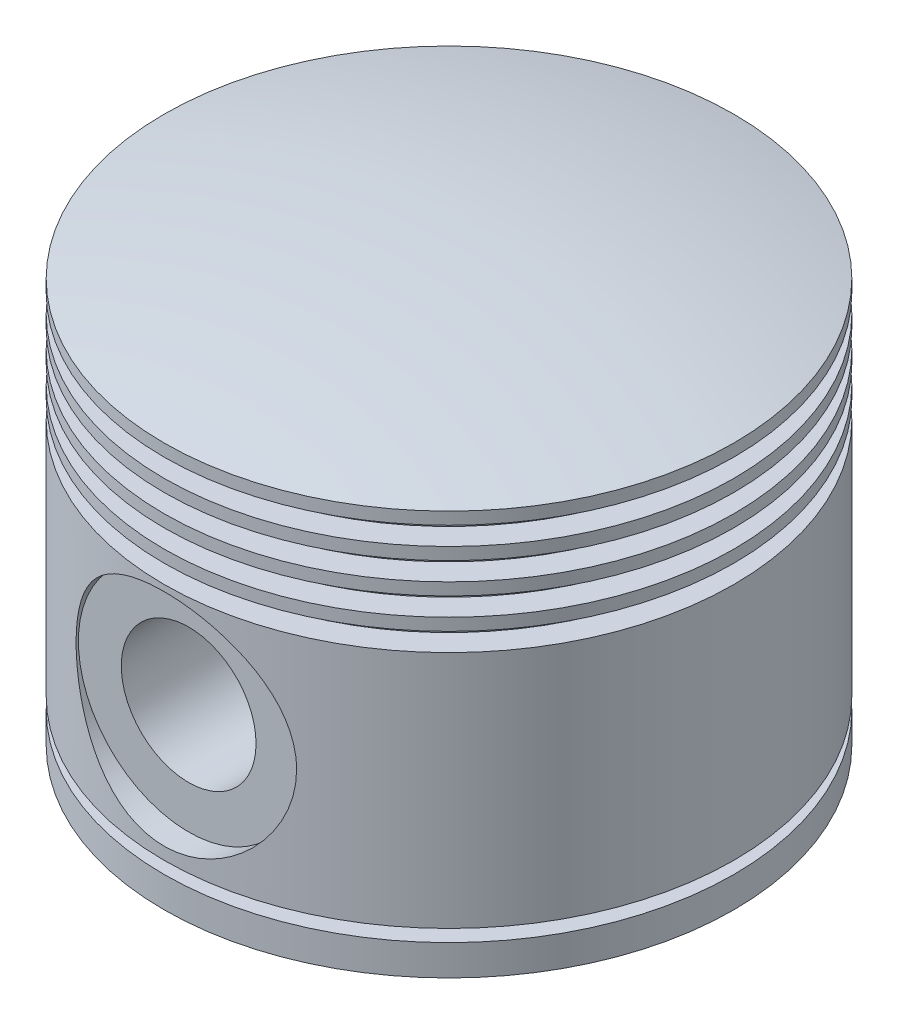
SolidWorks part; units mm, degrees
ref_plane "Front Plane" through (0, 0, 0) normal (0, 0, 1) x (1, 0, 0)
ref_plane "Top Plane" through (0, 0, 0) normal (0, 1, 0) x (1, 0, 0)
ref_plane "Right Plane" through (0, 0, 0) normal (1, 0, 0) x (0, 0, -1)
sketch "Sketch1" plane through (0, 0, 0) normal (0, 0, 1) x (1, 0, 0)
  line L0 (0, 0) -> (-2.4094, 0)
  line L1 (-46.5, 0) -> (-46.5, 5)
  line L2 (-46.5, 5) -> (-42.5, 5)
  line L3 (-42.5, 5) -> (-42.5, 7)
  line L4 (-42.5, 7) -> (-46.5, 7)
  line L5 (-46.5, 0) -> (-37, 0)
  line L6 (-37, 0) -> (-46.5, 0)
  line L7 (0, -1000) -> (0, 0) construction
  line L10 (-46.5, 7) -> (-46.5, 46)
  line L11 (-46.5, 46) -> (-42.5, 46)
  line L12 (-1042.5, 26.808) -> (-42.5, 26.808) construction
  line L15 (-42.5, 46) -> (-42.5, 49)
  line L16 (-42.5, 49) -> (-46.5, 49)
  line L17 (-46.5, 49) -> (-46.5, 51)
  line L18 (-46.5, 51) -> (-42.5, 51)
  line L19 (-42.5, 51) -> (-42.5, 54)
  line L20 (-42.5, 54) -> (-46.5, 54)
  line L21 (-46.5, 54) -> (-46.5, 56)
  line L22 (-46.5, 56) -> (-42.5, 56)
  line L23 (-42.5, 56) -> (-42.5, 59)
  line L24 (-42.5, 59) -> (-46.5, 59)
  line L25 (-46.5, 59) -> (-46.5, 61)
  line L26 (-46.5, 61) -> (-42.5, 61)
  line L27 (-42.5, 61) -> (-42.5, 64)
  line L28 (-42.5, 64) -> (-46.5, 64)
  line L29 (-46.5, 64) -> (-46.5, 66)
  line L30 (0, 62) -> (-37, 62)
  line L31 (0, 71.8095) -> (0, 62)
  line L32 (-37, 62) -> (-37, 0)
  line L40 (0, 62) -> (0, 82846.2829) construction
  arc A0 (-46.5, 66) -> (0, 71.8095) centre (0, -117.1905) cw
  point P5 (-37, 0.2055)
  point P7 (-42.5, 52.5)
  point P8 (0, 0)
  dimension "D17" = 189
  dimension "D1" = 42.5
  dimension "D2" = 4
  dimension "D3" = 2
  dimension "D4" = 7
  dimension "D5" = 39
  dimension "D6" = 46.5
  dimension "D7" = 42.5
  dimension "D8" = 42.5
  dimension "D9" = 3
  dimension "D10" = 3
  dimension "D11" = 3
  dimension "D12" = 2
  dimension "D13" = 2
  dimension "D14" = 2
  dimension "D15" = 3
  dimension "D16" = 2
  dimension "D18" = 62
  dimension "D19" = 37
  dimension "D20" = 42.5
  dimension "D21" = 42.5
revolve "Revolve3" add sketch "Sketch1" angle 360 about L31
ref_plane "Plane3" through (0, 0, 46.5) normal (0, 0, 1) x (1, 0, 0)
sketch "Sketch6" plane through (0, 0, 46.5) normal (0, 0, 1) x (1, 0, 0)
  circle A0 centre (0, 27) radius 18
  dimension "D2" = 36
  dimension "D1" = 27
extrude "Cut-Extrude11" cut sketch "Sketch6" against normal blind 4
sketch "Sketch7" plane through (0, 0, 42.5) normal (0, 0, 1) x (1, 0, 0)
  circle A0 centre (0, 27) radius 11
  dimension "D1" = 22
extrude "Cut-Extrude12" cut sketch "Sketch7" against normal up to next
sketch "Sketch11" plane through (0, 0, 42.5) normal (0, 0, 1) x (1, 0, 0)
  circle A0 centre (0, 27) radius 11 construction
  circle A1 centre (0, 27) radius 18 construction
  circle A2 centre (0, 27) radius 11
  circle A3 centre (0, 27) radius 18
extrude "Boss-Extrude1" add sketch "Sketch11" against normal blind 17.5
mirror "Mirror1" about plane through (0, 0, 0) normal (0, 0, 1) of "Boss-Extrude1", "Cut-Extrude12", "Cut-Extrude11"
